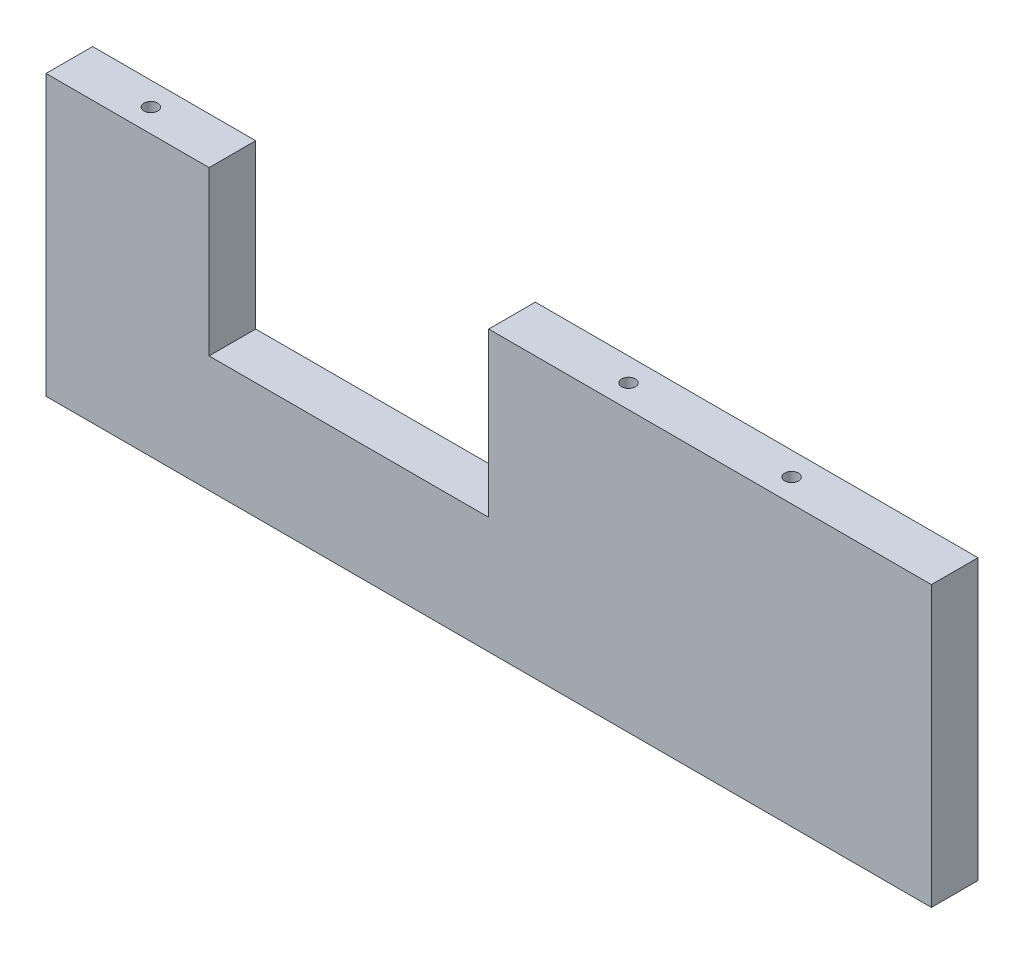
SolidWorks part; units mm, degrees
ref_plane "Front Plane" through (0, 0, 0) normal (0, 0, 1) x (1, 0, 0)
ref_plane "Top Plane" through (0, 0, 0) normal (0, 1, 0) x (1, 0, 0)
ref_plane "Right Plane" through (0, 0, 0) normal (1, 0, 0) x (0, 0, -1)
sketch "Sketch2" plane through (0, 0, 0) normal (0, 0, 1) x (1, 0, 0)
  line L1 (-95, 30) -> (95, 30)
  line L2 (-95, 30) -> (-95, -30)
  line L3 (-95, -30) -> (95, -30)
  line L4 (95, 30) -> (95, -30)
  line L5 (-95, 30) -> (95, -30) construction
  line L6 (-95, -30) -> (95, 30) construction
  line L7 (-60, 65) -> (0, 65)
  line L8 (-60, 65) -> (-60, -5)
  line L9 (-60, -5) -> (0, -5)
  line L10 (0, 65) -> (0, -5)
  line L11 (-60, 65) -> (0, -5) construction
  line L12 (-60, -5) -> (0, 65) construction
  point P0 (0, 0)
  point P6 (-30, 30)
  dimension "D1" = 190
  dimension "D2" = 60
  dimension "D3" = 35
  dimension "D4" = 60
  dimension "D5" = 70
extrude "Boss-Extrude1" add sketch "Sketch2" along normal blind 10 contours L1 L10 L9 L8 L2 L3 L4
sketch "Sketch3" plane through (0, 30, 0) normal (0, 1, 0) x (1, 0, 0)
  line L0 (-95, -5) -> (95, -5)
  line L1 (-95, -10) -> (95, -10)
  line L2 (-95, -10) -> (-95, 0)
  line L3 (-95, 0) -> (95, 0)
  line L4 (95, -10) -> (95, 0)
  circle A0 centre (-77.5, -5) radius 1.475
  circle A1 centre (25, -5) radius 1.475
  circle A2 centre (60, -5) radius 1.475
  point P8 (-77.5, -5)
  point P11 (60, -5)
  point P12 (25, -5)
  dimension "D2" = 2.95
  dimension "D1" = 17.5
  dimension "D3" = 35
  dimension "D4" = 35
extrude "Cut-Extrude1" cut sketch "Sketch3" against normal through all contours L0 A0 | L0 A0 | L0 A2 | L0 A2 | L0 A1 | L0 A1
